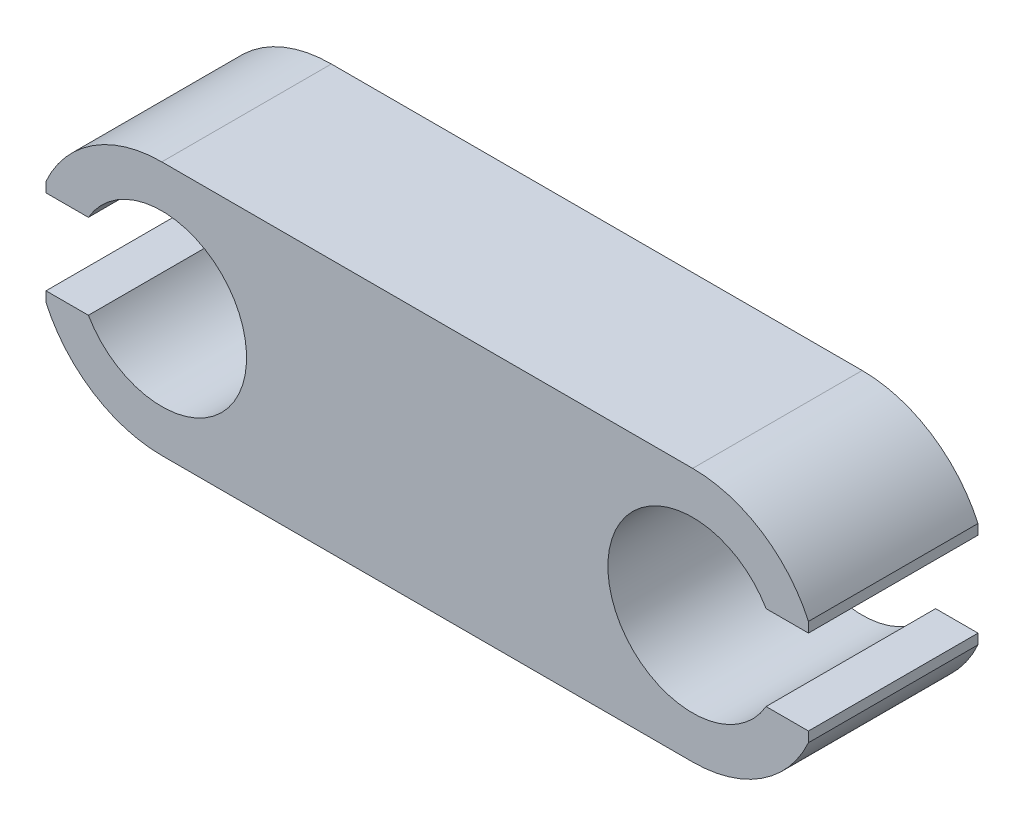
SolidWorks part; units mm, degrees
ref_plane "前视基准面" through (0, 0, 0) normal (0, 0, 1) x (1, 0, 0)
ref_plane "上视基准面" through (0, 0, 0) normal (0, 1, 0) x (1, 0, 0)
ref_plane "右视基准面" through (0, 0, 0) normal (1, 0, 0) x (0, 0, -1)
sketch "草图1" plane through (0, 0, 0) normal (0, 0, 1) x (1, 0, 0)
  line L0 (-140.9277, 0) -> (6905.455, 0) construction
  line L1 (0, -140.9277) -> (0, 6905.455) construction
  line L2 (-3.1311, 1.5) -> (3.1311, 1.5)
  line L3 (-3.1311, -1.5) -> (3.1311, -1.5)
  circle A0 centre (-3.1311, 0) radius 1.5
  circle A1 centre (3.1311, 0) radius 1.5
  point P12 (0, -1.5)
  point P15 (0, 1.5)
  dimension "D1" = 3
  dimension "D2" = 6.2622
extrude "凸台-拉伸1" add sketch "草图1" along normal blind 2 contours A0 | L3 A1 L2 A0 | A1
sketch "草图2" plane through (0, 0, 2) normal (0, 0, 1) x (1, 0, 0)
  line L0 (-1000, 0) -> (49000, 0) construction
  line L1 (0, -1000) -> (0, 49000) construction
  line L2 (-3.9971, -0.5) -> (-4.4971, -0.5)
  line L3 (-3.9971, 0.5) -> (-4.4971, 0.5)
  line L4 (3.9971, 0.5) -> (4.4971, 0.5)
  line L5 (-4.4971, -0.5) -> (-4.4971, -0.6197)
  line L6 (-4.4971, 0.5) -> (-4.4971, 0.6197)
  line L7 (3.9971, -0.5) -> (4.4971, -0.5)
  line L8 (4.4971, -0.5) -> (4.4971, -0.6197)
  line L9 (4.4971, 0.5) -> (4.4971, 0.6197)
  arc A0 (-3.9971, -0.5) -> (-3.9971, 0.5) centre (-3.1311, 0) ccw
  arc A1 (-3.1311, 1.5) -> (-3.1311, -1.5) centre (-3.1311, 0) ccw construction
  arc A2 (-4.4971, 0.6197) -> (-4.4971, -0.6197) centre (-3.1311, 0) ccw
  arc A3 (3.9971, -0.5) -> (3.9971, 0.5) centre (3.1311, 0) cw
  arc A4 (4.4971, 0.6197) -> (4.4971, -0.6197) centre (3.1311, 0) cw
  dimension "D1" = 2
  dimension "D2" = 0.5
extrude "切除-拉伸1" cut sketch "草图2" against normal blind 3
